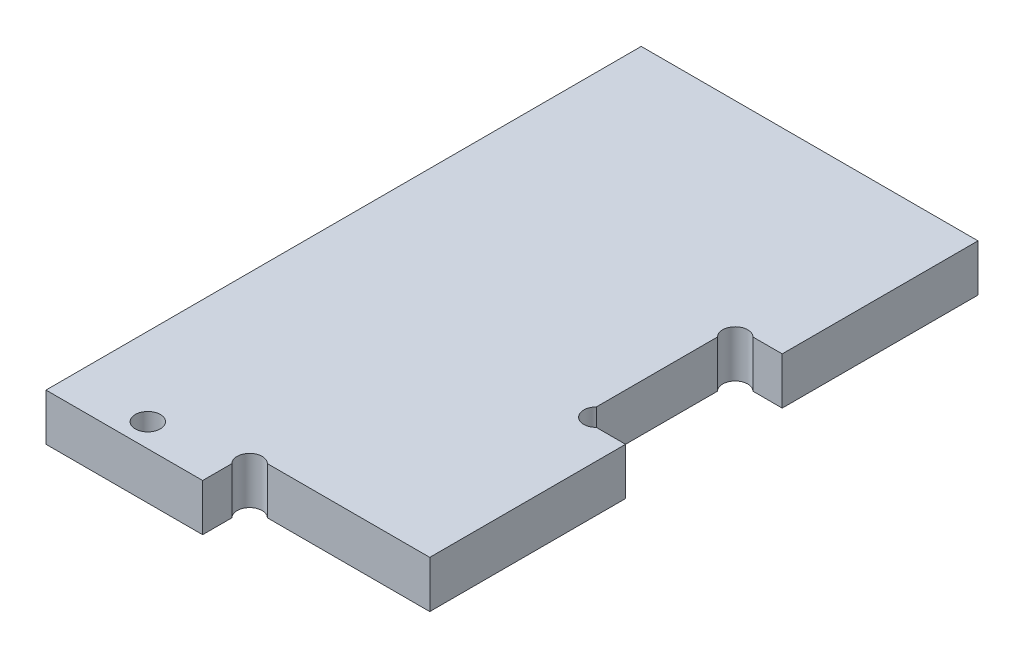
SolidWorks part; units mm, degrees
ref_plane "Plan de face" through (0, 0, 0) normal (0, 0, 1) x (1, 0, 0)
ref_plane "Plan de dessus" through (0, 0, 0) normal (0, 1, 0) x (1, 0, 0)
ref_plane "Plan de droite" through (0, 0, 0) normal (1, 0, 0) x (0, 0, -1)
sketch "Esquisse1" plane through (0, 0, 0) normal (0, 1, 0) x (1, 0, 0)
  line L0 (-17.765, 0) -> (114.7922, 0) construction
  line L1 (0, -29.8421) -> (0, 99.4612) construction
  line L2 (43, -29.8421) -> (43, 99.4612) construction
  line L3 (-17.765, 76) -> (114.7922, 76) construction
  line L4 (37, 86.6905) -> (37, -9.7282) construction
  line L5 (98.161, 6) -> (-6.878, 6) construction
  line L6 (20, 20.5911) -> (20, -28.198) construction
  line L7 (10, 19.2274) -> (10, -9.7282) construction
  line L8 (-4.1727, 3) -> (17.4945, 3) construction
  line L9 (80.2233, 41) -> (38.4041, 41) construction
  line L10 (80.2233, 31) -> (38.4041, 31) construction
  line L11 (37, 31) -> (51.1568, 45.1568) construction
  line L12 (20, 6) -> (40.2304, -14.2304) construction
  line L13 (39.2627, 31) -> (43, 31)
  line L14 (43, 31) -> (43, 6)
  line L15 (43, 6) -> (22.2627, 6)
  line L16 (37, 33.2627) -> (37, 48.7373)
  line L17 (20, 3.7373) -> (20, 0)
  line L18 (20, 0) -> (0, 0)
  line L19 (0, 0) -> (0, 76)
  line L20 (0, 76) -> (43, 76)
  line L21 (43, 76) -> (43, 51)
  line L22 (43, 51) -> (39.2627, 51)
  circle A0 centre (10, 3) radius 1.6
  arc A1 (22.2627, 6) -> (20, 3.7373) centre (21.1314, 4.8686) ccw
  arc A2 (37, 33.2627) -> (39.2627, 31) centre (38.1314, 32.1314) ccw
  arc A3 (37, 48.7373) -> (39.2627, 51) centre (38.1314, 49.8686) cw
  dimension "D10" = 3
  dimension "D11" = 45
  dimension "D1" = 43
  dimension "D2" = 76
  dimension "D3" = 6
  dimension "D4" = 6
  dimension "D5" = 35
  dimension "D6" = 10
  dimension "D7" = 45
  dimension "D8" = 23
  dimension "D9" = 10
extrude "Boss.-Extru.1" add sketch "Esquisse1" along normal blind 6
